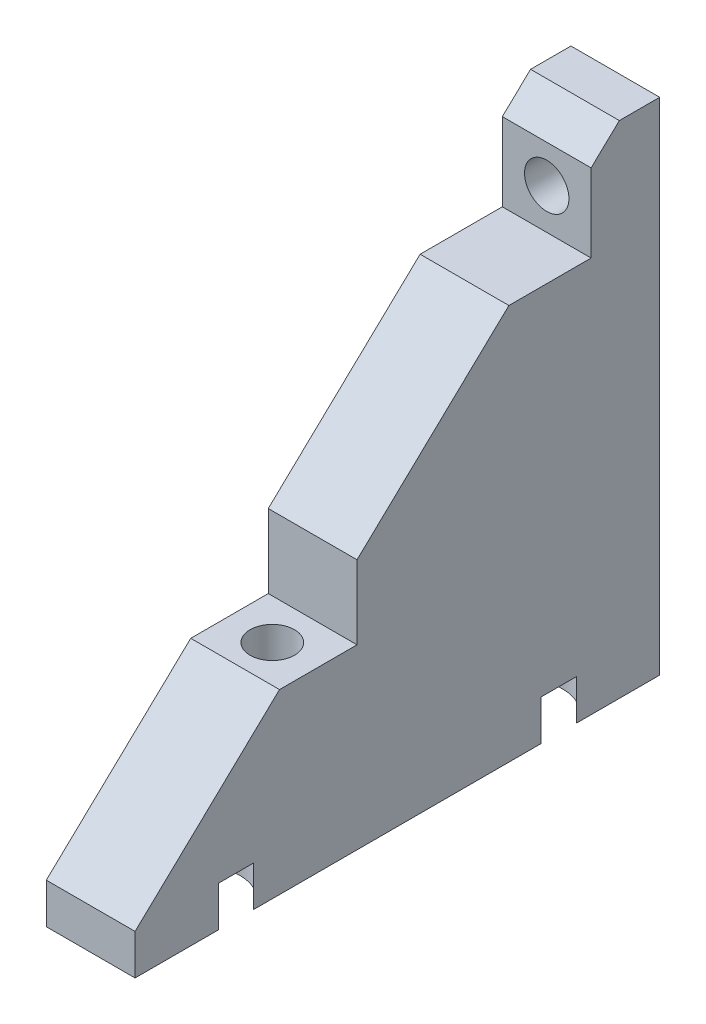
SolidWorks part; units mm, degrees
ref_plane "Front Plane" through (0, 0, 0) normal (0, 0, 1) x (1, 0, 0)
ref_plane "Top Plane" through (0, 0, 0) normal (0, 1, 0) x (1, 0, 0)
ref_plane "Right Plane" through (0, 0, 0) normal (1, 0, 0) x (0, 0, -1)
sketch "Sketch1" plane through (0, 0, 0) normal (0, 0, 1) x (1, 0, 0)
  line L0 (0, 0) -> (0, -161.0316) construction
  line L1 (-32.5, -137) -> (32.5, -137)
  line L2 (-32.5, -137) -> (-32.5, -80)
  line L3 (-32.5, -80) -> (32.5, -80)
  line L4 (32.5, -137) -> (32.5, -80)
  line L5 (0, -100) -> (0, -80) construction
  circle A1 centre (0, 0) radius 100 construction
  point P7 (0, -80)
  dimension "D2" = 20
  dimension "D1" = 10
  dimension "D3" = 65
extrude "Boss-Extrude1" add sketch "Sketch1" against normal blind 5
sketch "Sketch2" plane through (0, -137, 0) normal (0, -1, 0) x (1, 0, 0)
  line L0 (32.5, -5) -> (32.5, 0) construction
  line L1 (-32.5, -5) -> (32.5, -5)
  line L2 (-32.5, -5) -> (-32.5, 60)
  line L3 (-32.5, 60) -> (32.5, 60)
  line L4 (32.5, -5) -> (32.5, 60)
  line L5 (0, 60) -> (0, 0) construction
  line L6 (32.5, 27.5) -> (-32.5, 27.5) construction
  line L7 (21, 47.5) -> (-20, 47.5) construction
  circle A0 centre (20, 37.5) radius 2.75
  circle A1 centre (21, 47.5) radius 5
  circle A4 centre (-20, 47.5) radius 5
  circle A5 centre (-20, 7.5) radius 5
  circle A6 centre (21, 7.5) radius 5
  circle A7 centre (-20, 37.5) radius 2.75
  dimension "D3" = 5.5
  dimension "D6" = 10
  dimension "D9" = 10
  dimension "D1" = 65
  dimension "D2" = 12.5
  dimension "D4" = 22.5
  dimension "D5" = 12.5
  dimension "D7" = 21
  dimension "D8" = 20
extrude "Boss-Extrude2" add sketch "Sketch2" along normal blind 5
sketch "Sketch3" plane through (0, -137, 0) normal (0, 1, 0) x (1, 0, 0)
  line L6 (32.5, 0) -> (-32.5, 0) construction
  line L7 (25.5, 0) -> (14.5, 0)
  line L9 (0, 0) -> (0, -67.5782) construction
  line L14 (25.5, 0) -> (25.5, -60)
  line L15 (25.5, -60) -> (14.5, -60)
  line L16 (14.5, 0) -> (14.5, -60)
  line L17 (32.5, -60) -> (-32.5, -60) construction
  line L18 (20, -37.5) -> (14.5, -37.5) construction
  line L19 (20, -37.5) -> (25.5, -37.5) construction
  line L20 (-25.5, 0) -> (-14.5, 0)
  line L21 (-25.5, 0) -> (-25.5, -60)
  line L22 (-14.5, 0) -> (-14.5, -60)
  line L23 (-25.5, -60) -> (-14.5, -60)
  dimension "D1" = 5.5
extrude "Boss-Extrude7" add sketch "Sketch3" along normal up to surface (57 mm away) up to face at (0, -80, -2.5)
sketch "Sketch5" plane through (25.5, 0, 0) normal (1, 0, 0) x (0, 0, -1)
  line L0 (-60, -137) -> (0, -80)
  line L1 (0, -80) -> (-60, -80)
  line L2 (-60, -80) -> (-60, -137)
extrude "Cut-Extrude2" cut sketch "Sketch5" against normal through all
sketch "Sketch6" plane through (0, -137, 0) normal (0, -1, 0) x (1, 0, 0)
  circle A0 centre (-20, 37.5) radius 2.75 construction
  circle A1 centre (20, 37.5) radius 2.75 construction
  circle A2 centre (-20, 37.5) radius 2.75
  circle A3 centre (20, 37.5) radius 2.75
extrude "Cut-Extrude3" cut sketch "Sketch6" against normal through all
sketch "Sketch7" plane through (0, 0, 60) normal (0, 0, 1) x (1, 0, 0)
  line L0 (-20, -137) -> (-20, -73.184) construction
  line L1 (-25.5, -137) -> (-14.5, -137) construction
  line L2 (0, -142) -> (0, -80) construction
  line L3 (32.5, -142) -> (-32.5, -142) construction
  line L4 (14.5, -80) -> (-14.5, -80) construction
  line L5 (-25.5, -80) -> (-14.5, -80) construction
  circle A1 centre (-20, -88) radius 2.75
  circle A2 centre (20, -88) radius 2.75
  dimension "D1" = 5.5
  dimension "D2" = 8
extrude "Cut-Extrude4" cut sketch "Sketch7" against normal through all
sketch "Sketch8" plane through (0, -137, 0) normal (0, 1, 0) x (1, 0, 0)
  line L0 (25.5, -60) -> (25.5, 0) construction
  line L1 (25.5, -42.5) -> (14.5, -42.5)
  line L2 (25.5, -42.5) -> (25.5, -32.5)
  line L3 (25.5, -32.5) -> (14.5, -32.5)
  line L4 (14.5, -42.5) -> (14.5, -32.5)
  line L5 (14.5, -60) -> (14.5, 0) construction
  line L6 (25.5, -42.5) -> (14.5, -32.5) construction
  line L7 (0, 0) -> (0, -60) construction
  line L8 (14.5, 0) -> (-14.5, 0) construction
  line L9 (14.5, -60) -> (-14.5, -60) construction
  line L10 (-25.5, -42.5) -> (-25.5, -32.5)
  line L11 (-25.5, -32.5) -> (-14.5, -32.5)
  line L12 (-14.5, -42.5) -> (-14.5, -32.5)
  line L13 (-25.5, -42.5) -> (-14.5, -42.5)
  point P8 (20, -37.5)
  dimension "D1" = 10
extrude "Cut-Extrude5" cut sketch "Sketch8" against normal blind 40 from surface at 57 starting at face at (0, -80, -1.25)
sketch "Sketch9" plane through (0, 0, 0) normal (0, 0, 1) x (1, 0, 0)
  line L0 (-14.5, -80) -> (-14.5, -110.875) construction
  line L1 (-14.5, -93) -> (-25.5, -93)
  line L2 (-14.5, -93) -> (-14.5, -83)
  line L3 (-14.5, -83) -> (-25.5, -83)
  line L4 (-25.5, -93) -> (-25.5, -83)
  line L5 (-25.5, -110.875) -> (-25.5, -80) construction
  line L6 (0, -137) -> (0, -80) construction
  line L7 (14.5, -137) -> (-14.5, -137) construction
  line L8 (14.5, -80) -> (-14.5, -80) construction
  line L9 (-25.5, -93) -> (-14.5, -83) construction
  line L10 (25.5, -93) -> (25.5, -83)
  line L11 (14.5, -93) -> (25.5, -93)
  line L12 (14.5, -83) -> (25.5, -83)
  line L13 (14.5, -93) -> (14.5, -83)
  point P14 (-20, -88)
  point P17 (-20, -88)
  dimension "D1" = 10
extrude "Cut-Extrude6" cut sketch "Sketch9" against normal blind 56.5 from surface at 60 starting at face at (0, -138.25, 60)
sketch "Sketch10" plane through (0, 0, 60) normal (0, 0, 1) x (1, 0, 0)
  line L0 (32.5, -142) -> (-32.5, -142) construction
  line L1 (-32.5, -80) -> (-25.5, -80)
  line L2 (-32.5, -80) -> (-32.5, -142)
  line L3 (-32.5, -142) -> (-25.5, -142)
  line L4 (-25.5, -80) -> (-25.5, -142)
  line L5 (25.5, -137) -> (25.5, -120) construction
  line L6 (-14.5, -80) -> (14.5, -80)
  line L7 (-14.5, -80) -> (-14.5, -142)
  line L8 (-14.5, -142) -> (14.5, -142)
  line L9 (14.5, -80) -> (14.5, -142)
  line L10 (32.5, -80) -> (25.5, -80)
  line L11 (32.5, -80) -> (32.5, -142)
  line L12 (32.5, -142) -> (25.5, -142)
  line L13 (25.5, -80) -> (25.5, -142)
  line L15 (-25.5, -137) -> (-25.5, -120) construction
  line L16 (14.5, -137) -> (14.5, -120) construction
extrude "Cut-Extrude7" cut sketch "Sketch10" against normal through all
delete or keep bodies "Body-Delete/Keep 1" type keep bodies bodies 112
